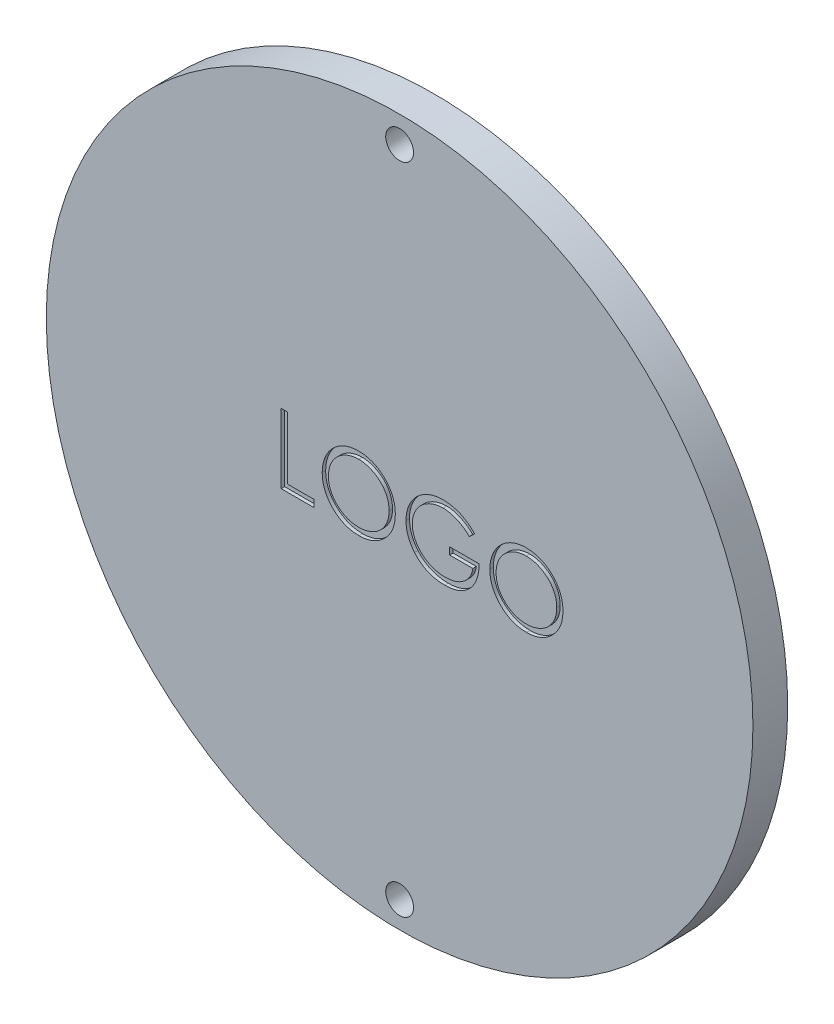
SolidWorks part; units mm, degrees
ref_plane "Plan de face" through (0, 0, 0) normal (0, 0, 1) x (1, 0, 0)
ref_plane "Plan de dessus" through (0, 0, 0) normal (0, 1, 0) x (1, 0, 0)
ref_plane "Plan de droite" through (0, 0, 0) normal (1, 0, 0) x (0, 0, -1)
sketch "Esquisse1" plane through (0, 0, 0) normal (0, 0, 1) x (1, 0, 0)
  circle A0 centre (0, 0) radius 50.8
  dimension "D1" = 101.6
extrude "Boss.-Extru.1" add sketch "Esquisse1" along normal blind 5
sketch "Esquisse2" plane through (0, 0, 5) normal (0, 0, 1) x (1, 0, 0)
  line L0 (0, -55) -> (0, 55) construction
  circle A0 centre (0, 47) radius 2
  circle A1 centre (0, -47) radius 2
  point P10 (0, 0)
  dimension "D1" = 4
  dimension "D2" = 47
  dimension "D3" = 2
extrude "Enlèv. mat.-Extru.1" cut sketch "Esquisse2" against normal through all
sketch "Esquisse4" plane through (0, 0, 5) normal (0, 0, 1) x (1, 0, 0)
  text T0 "LOGO" font "Century Gothic" height 10
extrude "Enlèv. mat.-Extru.2" cut sketch "Esquisse4" against normal blind 0.5
